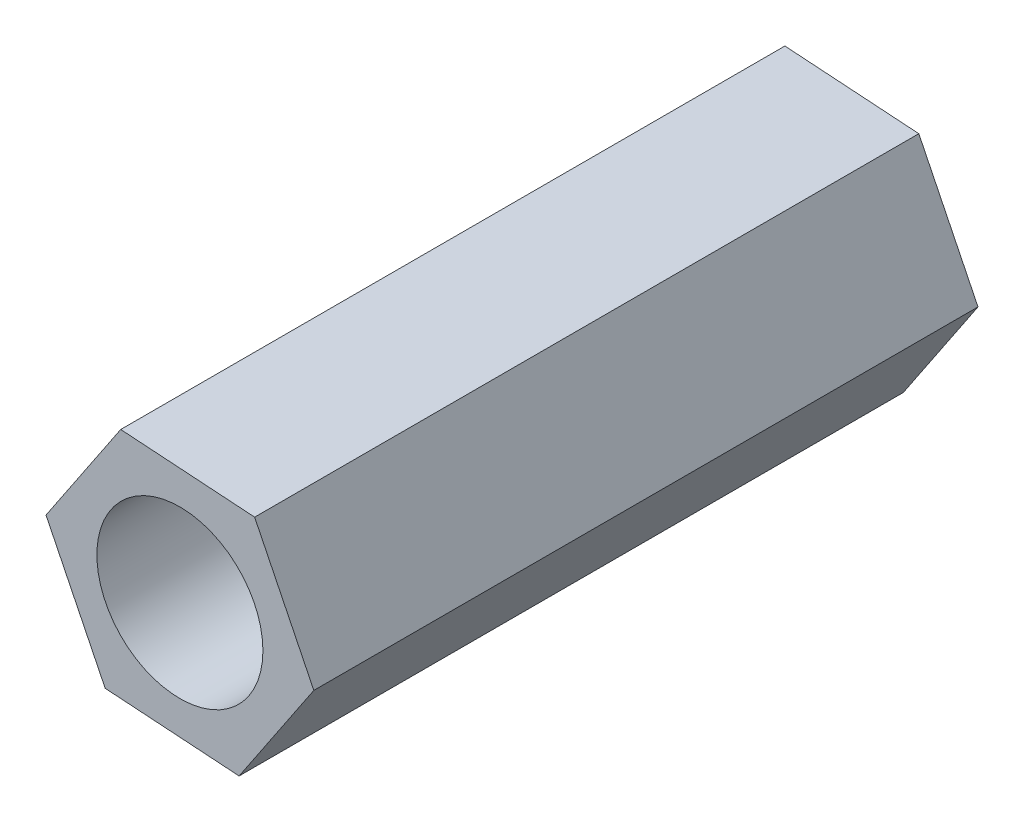
SolidWorks part; units mm, degrees
ref_plane "Front Plane" through (0, 0, 0) normal (0, 0, 1) x (1, 0, 0)
ref_plane "Top Plane" through (0, 0, 0) normal (0, 1, 0) x (1, 0, 0)
ref_plane "Right Plane" through (0, 0, 0) normal (1, 0, 0) x (0, 0, -1)
sketch "Sketch1" plane through (0, 0, 0) normal (0, 0, 1) x (1, 0, 0)
  line L1 (1.7823, -3.6272) -> (4.0324, -0.2701)
  line L2 (4.0324, -0.2701) -> (2.2501, 3.3571)
  line L3 (2.2501, 3.3571) -> (-1.7823, 3.6272)
  line L4 (-1.7823, 3.6272) -> (-4.0324, 0.2701)
  line L5 (-4.0324, 0.2701) -> (-2.2501, -3.3571)
  line L6 (-2.2501, -3.3571) -> (1.7823, -3.6272)
  circle A0 centre (0, 0) radius 2.5
  circle A1 centre (0, 0) radius 3.5 construction
  dimension "D1" = 5
  dimension "D2" = 7
extrude "Boss-Extrude1" add sketch "Sketch1" along normal blind 20
